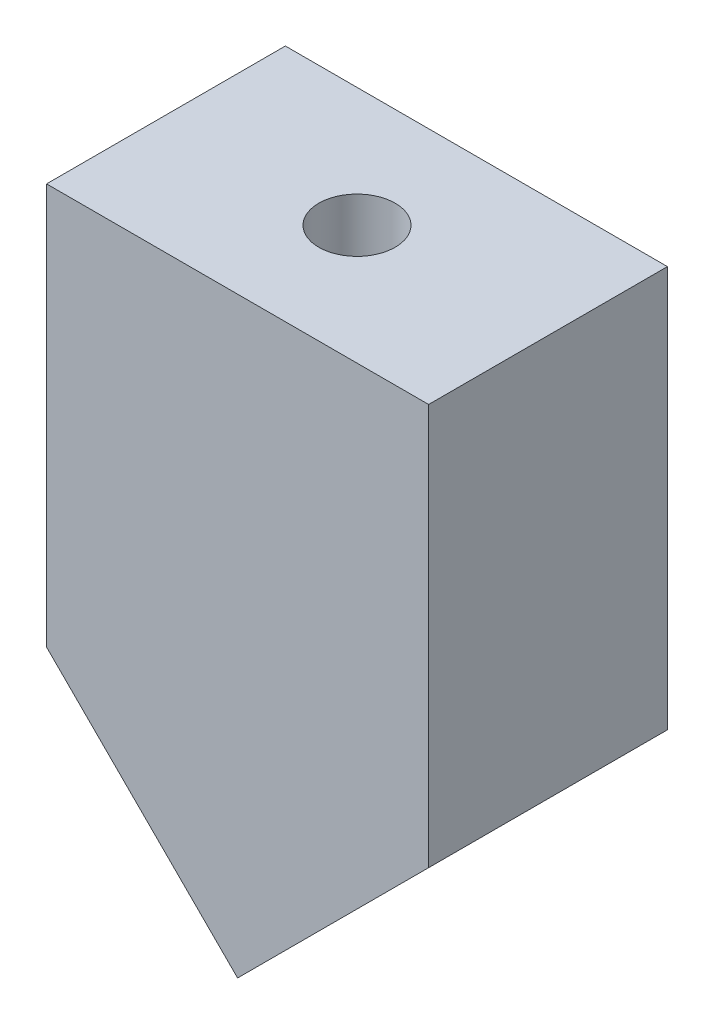
SolidWorks part; units mm, degrees
ref_plane "Front Plane" through (0, 0, 0) normal (0, 0, 1) x (1, 0, 0)
ref_plane "Top Plane" through (0, 0, 0) normal (0, 1, 0) x (1, 0, 0)
ref_plane "Right Plane" through (0, 0, 0) normal (1, 0, 0) x (0, 0, -1)
sketch "Sketch1" plane through (0, 0, 0) normal (0, 0, 1) x (1, 0, 0)
  line L0 (0, 0) -> (0, 30164.2219) construction
  line L1 (0, 0) -> (-30164.2219, 0) construction
  line L3 (20, -31) -> (-20, -31)
  line L4 (20, -31) -> (20, 31)
  line L5 (20, 31) -> (-20, 31)
  line L6 (-20, -31) -> (-20, 31)
  line L7 (20, -31) -> (-20, 31) construction
  line L8 (20, 31) -> (-20, -31) construction
  point P5 (0, 0)
  dimension "D1" = 62
  dimension "D2" = 40
extrude "Boss-Extrude1" add sketch "Sketch1" along normal blind 25
sketch "Sketch2" plane through (0, 0, 25) normal (0, 0, 1) x (1, 0, 0)
  line L0 (0, 0) -> (0, 50000) construction
  line L1 (0, -31) -> (-20, -11)
  line L2 (0, 0) -> (-50000, 0) construction
  line L3 (-20, -31) -> (20, -31) construction
  line L6 (-20, 31) -> (-20, -31) construction
  line L8 (0, -31) -> (20, -11)
  line L9 (-20, -11) -> (-20, -38.533)
  line L10 (-20, -38.533) -> (20, -38.533)
  line L11 (20, -38.533) -> (20, -11)
  dimension "D1" = 45
extrude "Cut-Extrude1" cut sketch "Sketch2" against normal blind 25
sketch "Sketch3" plane through (0, 31, 0) normal (0, 1, 0) x (1, 0, 0)
  line L0 (0, 0) -> (0, 50000) construction
  line L3 (-20, -12.5) -> (-50020, -12.5) construction
  line L6 (20, -25) -> (-20, -25) construction
  circle A0 centre (0, -12.5) radius 4
  dimension "D2" = 8
  dimension "D1" = 12.5
extrude "Cut-Extrude2" cut sketch "Sketch3" against normal blind 30
